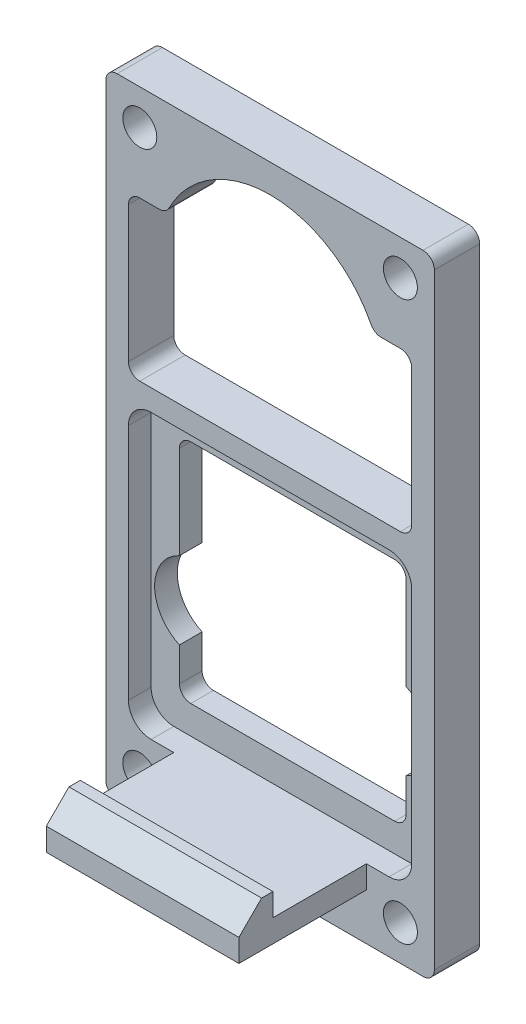
SolidWorks part; units mm, degrees
material "ABS"
ref_plane "Front Plane" through (0, 0, 0) normal (0, 0, 1) x (1, 0, 0)
ref_plane "Top Plane" through (0, 0, 0) normal (0, 1, 0) x (1, 0, 0)
ref_plane "Right Plane" through (0, 0, 0) normal (1, 0, 0) x (0, 0, -1)
sketch "Sketch1" plane through (0, 0, 0) normal (0, 0, 1) x (1, 0, 0)
  line L1 (0, 0) -> (29, 0)
  line L2 (0, 0) -> (0, 55.5)
  line L3 (0, 55.5) -> (29, 55.5)
  line L4 (29, 0) -> (29, 55.5)
  dimension "D1" = 55.5
  dimension "D2" = 29
extrude "Body" add sketch "Sketch1" along normal blind 4
sketch "Sketch2" plane through (0, 0, 4) normal (0, 0, 1) x (1, 0, 0)
  line L0 (14.5, 55.5) -> (14.5, 0) construction
  line L1 (29, 55.5) -> (0, 55.5) construction
  line L2 (0, 0) -> (29, 0) construction
  line L3 (0, 27.75) -> (29, 27.75) construction
  line L4 (0, 55.5) -> (0, 0) construction
  line L5 (29, 0) -> (29, 55.5) construction
  circle A0 centre (3, 52.385) radius 1.5
  circle A1 centre (26, 52.385) radius 1.5
  circle A2 centre (26, 3.115) radius 1.5
  circle A3 centre (3, 3.115) radius 1.5
  dimension "D1" = 3
  dimension "D2" = 11.5
  dimension "D3" = 24.635
extrude "Bolt Holes" cut sketch "Sketch2" against normal through all
sketch "Sketch3" plane through (0, 0, 4) normal (0, 0, 1) x (1, 0, 0)
  line L0 (14.5, 55.5) -> (14.5, 0) construction
  line L1 (29, 55.5) -> (0, 55.5) construction
  line L2 (0, 0) -> (29, 0) construction
  line L3 (0, 27.75) -> (29, 27.75) construction
  line L4 (0, 55.5) -> (0, 0) construction
  line L5 (29, 0) -> (29, 55.5) construction
  line L6 (3, 3.115) -> (26, 3.115) construction
  line L7 (4.5, 12.5899) -> (4.5, 8.615)
  line L8 (24.5, 12.5899) -> (24.5, 8.615)
  line L9 (4.5, 43) -> (24.5, 43) construction
  line L10 (2, 47) -> (5.3348, 47)
  line L11 (2, 47) -> (2, 33)
  line L12 (4.5, 28.615) -> (24.5, 28.615)
  line L13 (4.5, 28.615) -> (4.5, 19.4101)
  line L14 (4.5, 8.615) -> (24.5, 8.615)
  line L15 (24.5, 28.615) -> (24.5, 19.4101)
  line L16 (2, 33) -> (27, 33)
  line L17 (27, 47) -> (27, 33)
  line L19 (23.6652, 47) -> (27, 47)
  circle A0 centre (14.5, 43) radius 10 construction
  circle A1 centre (6.06, 16) radius 3.75 construction
  circle A2 centre (22.94, 16) radius 3.75 construction
  arc A3 (4.5, 19.4101) -> (4.5, 12.5899) centre (6.06, 16) ccw
  arc A4 (24.5, 19.4101) -> (24.5, 12.5899) centre (22.94, 16) cw
  arc A5 (5.3348, 47) -> (23.6652, 47) centre (14.5, 43) cw
  dimension "D1" = 20
  dimension "D2" = 12.5
  dimension "D3" = 7.5
  dimension "D4" = 16
  dimension "D5" = 8.44
  dimension "D8" = 20
  dimension "D6" = 5.5
  dimension "D7" = 20
  dimension "D9" = 4
  dimension "D10" = 2
extrude "Servo Clearance" cut sketch "Sketch3" against normal through all
sketch "Sketch4" plane through (0, 0, 4) normal (0, 0, 1) x (1, 0, 0)
  line L0 (14.5, 0) -> (14.5, 55.5) construction
  line L1 (2, 31.115) -> (27, 31.115)
  line L2 (2, 31.115) -> (2, 6.115)
  line L3 (2, 6.115) -> (27, 6.115)
  line L4 (27, 31.115) -> (27, 6.115)
  line L5 (0, 0) -> (29, 0) construction
  line L6 (29, 55.5) -> (0, 55.5) construction
  line L7 (3, 3.115) -> (26, 3.115) construction
  dimension "D1" = 25
  dimension "D2" = 3
extrude "Fan Recess" cut sketch "Sketch4" against normal offset from surface (2 mm away) 2 up to face at (14.5, 43.3333, 0)
sketch "Sketch5" plane through (0, 0, 4) normal (0, 0, 1) x (1, 0, 0)
  line L0 (2, 6.115) -> (27, 6.115) construction
  line L1 (6, 6.115) -> (23, 6.115)
  line L2 (6, 6.115) -> (6, 4.115)
  line L3 (6, 4.115) -> (23, 4.115)
  line L4 (23, 6.115) -> (23, 4.115)
  line L5 (14.5, 0) -> (14.5, 55.5) construction
  line L6 (0, 0) -> (29, 0) construction
  line L7 (29, 55.5) -> (0, 55.5) construction
  line L8 (3, 3.115) -> (3, 6.115) construction
  line L9 (3, 3.115) -> (6, 3.115) construction
  line L10 (6, 3.115) -> (6, 4.115) construction
  dimension "D1" = 2
fillet "Clamp Fillets" radius 1 14 edges at (24.5, 8.615, 1) (4.5, 8.615, 1) (4.5, 28.615, 1) (24.5, 28.615, 1) (27, 33, 2) (2, 33, 2) (27, 47, 2) (23.6652, 47, 2) (5.3348, 47, 2) (2, 47, 2) (0, 55.5, 2) (29, 55.5, 2) (29, 0, 2) (0, 0, 2)
fillet "Fan Fillets" radius 2 4 edges at (27, 31.115, 3) (2, 31.115, 3) (27, 6.115, 3) (2, 6.115, 3)
extrude "Clamp Base" add sketch "Sketch5" along normal offset from surface (8.25 mm away) 10.25 up to face at (14.5, 18.615, 2) offset beyond the face yes
sketch "Sketch7" plane through (6, 0, 0) normal (-1, 0, 0) x (0, 0, 1)
  line L0 (12.25, 4.115) -> (15.25, 4.115)
  line L1 (15.25, 4.115) -> (15.25, 6.115)
  line L2 (15.25, 6.115) -> (13.25, 8.115)
  line L3 (13.25, 8.115) -> (12.25, 8.115)
  line L4 (12.25, 8.115) -> (12.25, 4.115)
  line L5 (12.25, 4.115) -> (12.25, 6.115) construction
  dimension "D1" = 3
  dimension "D2" = 2
  dimension "D3" = 1
  dimension "D4" = 4
extrude "Clamp Hook" add sketch "Sketch7" against normal up to surface (17 mm away) up to face at (23, 5.115, 8.125)
ref_point "Ref Center"
